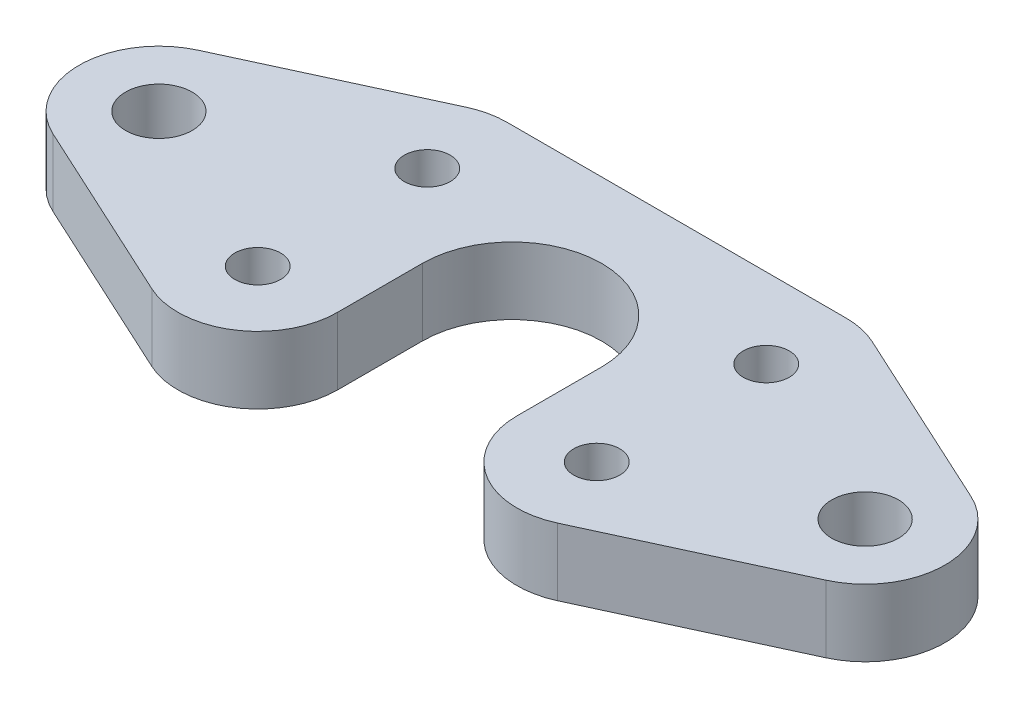
SolidWorks part; units mm, degrees
ref_plane "Front Plane" through (0, 0, 0) normal (0, 0, 1) x (1, 0, 0)
ref_plane "Top Plane" through (0, 0, 0) normal (0, 1, 0) x (1, 0, 0)
ref_plane "Right Plane" through (0, 0, 0) normal (1, 0, 0) x (0, 0, -1)
sketch "Sketch1" plane through (0, 0, 0) normal (0, 1, 0) x (1, 0, 0)
  line L0 (0, 6.35) -> (0, 11.65)
  line L2 (-12, -6) -> (0, 0) construction
  line L3 (0, 11.65) -> (-12, 11.65)
  line L5 (-6.35, 0) -> (-6.35, -6)
  line L6 (0, 0) -> (-12, 6) construction
  line L7 (-14.3677, -11.13) -> (-27.3677, -5.13)
  line L8 (-27.3677, 5.13) -> (-14.3677, 11.13)
  circle A0 centre (-25, 0) radius 2.36
  arc A1 (0, 6.35) -> (-6.35, 0) centre (0, 0) ccw
  circle A2 centre (-12, 6) radius 1.625
  circle A3 centre (-12, -6) radius 1.625
  arc A4 (-6.35, -6) -> (-14.3677, -11.13) centre (-12, -6) cw
  arc A5 (-27.3677, -5.13) -> (-27.3677, 5.13) centre (-25, 0) cw
  arc A6 (-14.3677, 11.13) -> (-12, 11.65) centre (-12, 6) cw
  dimension "D1" = 6.35
  dimension "D3" = 4.72
  dimension "D4" = 3.25
  dimension "D2" = 25
  dimension "D5" = 12
  dimension "D6" = 6
extrude "Boss-Extrude1" add sketch "Sketch1" along normal blind 4.7625
mirror "Mirror1" about plane through (0, 4.7625, -6.35) normal (-1, 0, 0) of "Boss-Extrude1"
